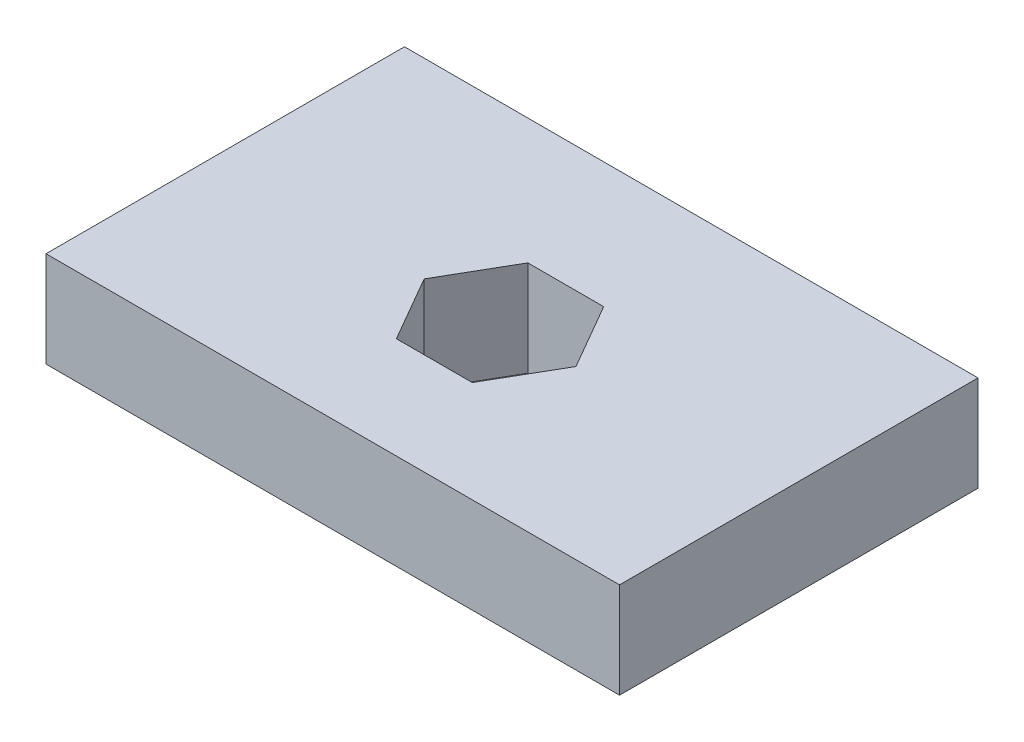
SolidWorks part; units mm, degrees
ref_plane "Front Plane" through (0, 0, 0) normal (0, 0, 1) x (1, 0, 0)
ref_plane "Top Plane" through (0, 0, 0) normal (0, 1, 0) x (1, 0, 0)
ref_plane "Right Plane" through (0, 0, 0) normal (1, 0, 0) x (0, 0, -1)
sketch "Sketch1" plane through (0, 0, 0) normal (0, 1, 0) x (1, 0, 0)
  line L0 (-38.1, 25.4) -> (38.1, 25.4)
  line L1 (10.082, 0) -> (5.041, 8.7313)
  line L2 (5.041, 8.7313) -> (-5.041, 8.7313)
  line L3 (-5.041, 8.7313) -> (-10.082, 0)
  line L4 (-10.082, 0) -> (-5.041, -8.7313)
  line L5 (-5.041, -8.7313) -> (5.041, -8.7313)
  line L6 (5.041, -8.7313) -> (10.082, 0)
  line L7 (38.1, 25.4) -> (38.1, -22.225)
  line L8 (38.1, -22.225) -> (-38.1, -22.225)
  line L9 (-38.1, -22.225) -> (-38.1, 25.4)
extrude "Boss-Extrude1" add sketch "Sketch1" along normal blind 12.7
sketch "Sketch2" plane through (0, 0, -25.4) normal (0, 0, -1) x (-1, 0, 0)
  circle A0 centre (-25.4, 6.35) radius 3.175
  circle A1 centre (25.4, 6.35) radius 3.175
extrude "Cut-Extrude1" cut sketch "Sketch2" against normal blind 25.4
